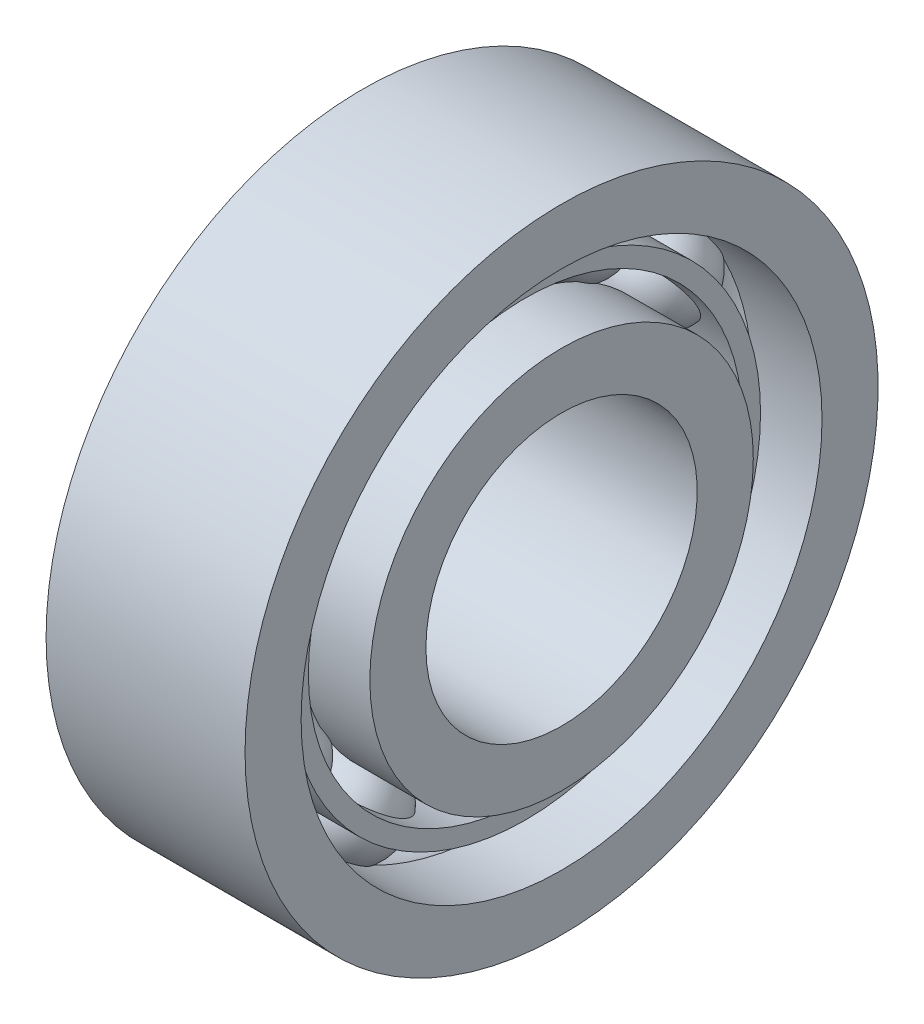
SolidWorks part; units mm, degrees
ref_plane "Plan de face" through (0, 0, 0) normal (0, 0, 1) x (1, 0, 0)
ref_plane "Plan de dessus" through (0, 0, 0) normal (0, 1, 0) x (1, 0, 0)
ref_plane "Plan de droite" through (0, 0, 0) normal (1, 0, 0) x (0, 0, -1)
sketch "Esquisse1" plane through (0, 0, 0) normal (0, 0, 1) x (1, 0, 0)
  line L0 (-5.5, 7.5) -> (5.5, 7.5)
  line L1 (5.5, 7.5) -> (5.5, 10.6)
  line L2 (5.5, 10.6) -> (1.6248, 10.6)
  line L3 (-5.5, 10.6) -> (-5.5, 7.5)
  line L4 (0, 0) -> (28.7577, 0) construction
  line L5 (-1.6248, 10.6) -> (-5.5, 10.6)
  arc A0 (-1.6248, 10.6) -> (1.6248, 10.6) centre (0, 12.5) ccw
  dimension "D5" = 12.5
  dimension "2" = 2.5
  dimension "D1" = 7.5
  dimension "D2" = 3.1
  dimension "D3" = 5.5
  dimension "D4" = 5.5
revolve "Révolution1" add sketch "Esquisse1" angle 360 about L4
sketch "Esquisse2" plane through (0, 0, 0) normal (0, 0, 1) x (1, 0, 0)
  line L0 (0, 15.1) -> (0, 9.9)
  arc A0 (0, 9.9) -> (0, 15.1) centre (0, 12.5) ccw
  dimension "D2" = 2.6
  dimension "D1" = 12.5
revolve "Révolution2" add sketch "Esquisse2" angle 360 about L0
pattern_circular "Répétition circulaire1" count 12 every 30 about axis through (0, 0, 0) along (1, 0, 0) of "Révolution2"
sketch "Esquisse3" plane through (0, 0, 0) normal (0, 0, 1) x (1, 0, 0)
  line L0 (1.6248, 14.4) -> (5.5, 14.4)
  line L1 (-5.5, 17.5) -> (5.5, 17.5)
  line L2 (-5.5, 17.5) -> (-5.5, 14.4)
  line L3 (-5.5, 14.4) -> (-1.6248, 14.4)
  line L4 (5.5, 17.5) -> (5.5, 14.4)
  line L5 (0, 0) -> (20.1307, 0) construction
  arc A0 (1.6248, 14.4) -> (-1.6248, 14.4) centre (0, 12.5) ccw
  dimension "D4" = 2.5
  dimension "D1" = 5.5
  dimension "D2" = 5.5
  dimension "D3" = 17.5
  dimension "D5" = 12.5
  dimension "D6" = 3.1
revolve "Révolution3" add sketch "Esquisse3" angle 360 about L5
sketch "Esquisse4" plane through (0, 0, 0) normal (0, 0, 1) x (1, 0, 0)
  line L0 (0, 0) -> (12.8903, 0) construction
  line L1 (-3.5, 13) -> (3.5, 13)
  line L2 (-3.5, 13) -> (-3.5, 12)
  line L3 (-3.5, 12) -> (3.5, 12)
  line L4 (3.5, 13) -> (3.5, 12)
  dimension "D1" = 12
  dimension "D2" = 13
  dimension "D3" = 3.5
  dimension "D4" = 3.5
revolve "Révolution4" add sketch "Esquisse4" angle 360 about L0
